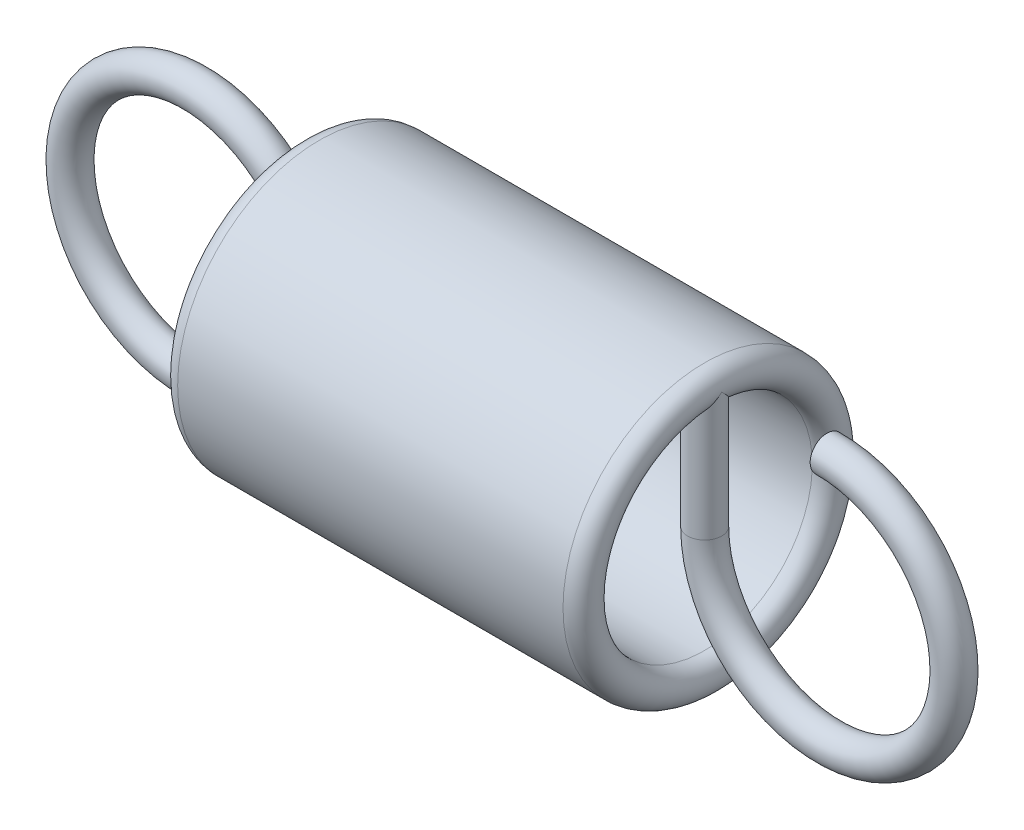
SolidWorks part; units mm, degrees
ref_plane "Front Plane" through (0, 0, 0) normal (0, 0, 1) x (1, 0, 0)
ref_plane "Top Plane" through (0, 0, 0) normal (0, 1, 0) x (1, 0, 0)
ref_plane "Right Plane" through (0, 0, 0) normal (1, 0, 0) x (0, 0, -1)
ref_plane "Plane1" through (0, 0, 0) normal (0, 0, 1) x (1, 0, 0)
sketch "Sketch1" plane through (0, 0, 0) normal (0, 0, 1) x (1, 0, 0)
  line L0 (4.1, 1.9) -> (10.9, 1.9)
  line L1 (10.9, 2.5) -> (4.1, 2.5)
  line L2 (11.2, 0) -> (3.8, 0) construction
  arc A0 (4.1, 2.5) -> (4.1, 1.9) centre (4.1, 2.2) ccw
  arc A1 (10.9, 1.9) -> (10.9, 2.5) centre (10.9, 2.2) ccw
revolve "Revolve1" add sketch "Sketch1" angle 360 about L2
ref_plane "Plane2" through (0, 0, 0) normal (0, 0, 1) x (1, 0, 0)
sketch "Sketch2" plane through (0, 0, 0) normal (0, 0, 1) x (1, 0, 0)
  line L0 (10.9, 2.2) -> (11.2, 2.2)
  line L1 (11.2, 2.2) -> (11.2, 0)
  line L2 (11.2, 0) -> (10.9, 0)
  line L3 (10.9, 0) -> (10.9, 2.2)
  line L4 (10.9, 0) -> (10.9, 2.2) construction
revolve "Revolve2" add sketch "Sketch2" angle 360 about L4
ref_plane "Plane3" through (0, 0, 0) normal (0, 1, 0) x (-1, 0, 0)
sketch "Sketch3" plane through (0, 0, 0) normal (0, 1, 0) x (-1, 0, 0)
  line L0 (-13.1, -2.5) -> (-13.1, 2.5) construction
  circle A0 centre (-10.9, 0) radius 0.3
revolve "Revolve3" add sketch "Sketch3" angle 271 about L0
ref_plane "Plane4" through (0, 0, 0) normal (0, 0, 1) x (1, 0, 0)
sketch "Sketch4" plane through (0, 0, 0) normal (0, 0, 1) x (1, 0, 0)
  line L0 (4.1, 0) -> (4.4, 0)
  line L1 (4.4, 0) -> (4.4, -2.2)
  line L2 (4.4, -2.2) -> (4.1, -2.2)
  line L3 (4.1, -2.2) -> (4.1, 0)
  line L4 (4.1, -2.2) -> (4.1, 0) construction
revolve "Revolve4" add sketch "Sketch4" angle 360 about L4
ref_plane "Plane5" through (0, 0, 0) normal (0, 1, 0) x (-1, 0, 0)
sketch "Sketch5" plane through (0, 0, 0) normal (0, 1, 0) x (-1, 0, 0)
  line L0 (-1.9, 2.5) -> (-1.9, -2.5) construction
  circle A0 centre (-4.1, 0) radius 0.3
revolve "Revolve5" add sketch "Sketch5" angle 271 about L0
